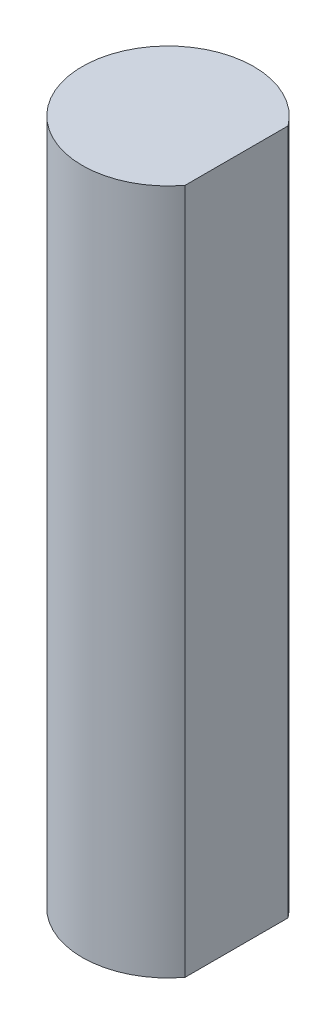
SolidWorks part; units mm, degrees
ref_plane "Front Plane" through (0, 0, 0) normal (0, 0, 1) x (1, 0, 0)
ref_plane "Top Plane" through (0, 0, 0) normal (0, 1, 0) x (1, 0, 0)
ref_plane "Right Plane" through (0, 0, 0) normal (1, 0, 0) x (0, 0, -1)
sketch "Sketch1" plane through (0, 0, 0) normal (0, 1, 0) x (1, 0, 0)
  line L0 (0, 0) -> (2.54, 0) construction
  line L1 (2.54, 3.81) -> (2.54, -3.81)
  circle A0 centre (0, 0) radius 3.175
  point P6 (2.54, 0)
  dimension "D1" = 6.35
  dimension "D2" = 2.54
  dimension "D3" = 7.62
extrude "Boss-Extrude1" add sketch "Sketch1" along normal blind 25.4
equation "\"D2@Sketch1\"=.125-.025"
